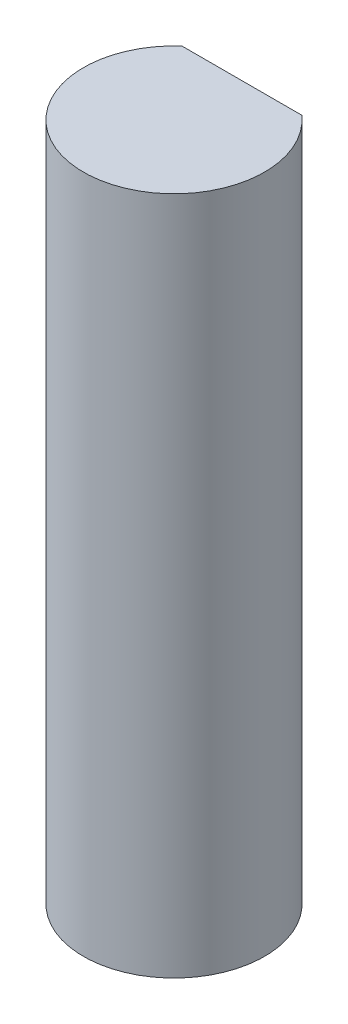
SolidWorks part; units mm, degrees
ref_plane "Front Plane" through (0, 0, 0) normal (0, 0, 1) x (1, 0, 0)
ref_plane "Top Plane" through (0, 0, 0) normal (0, 1, 0) x (1, 0, 0)
ref_plane "Right Plane" through (0, 0, 0) normal (1, 0, 0) x (0, 0, -1)
sketch "Sketch1" plane through (0, 0, 0) normal (0, 1, 0) x (1, 0, 0)
  line L0 (-1.3229, 1.5) -> (1.3229, 1.5)
  line L2 (0, 0) -> (3.486, 0) construction
  arc A0 (-1.3229, 1.5) -> (1.3229, 1.5) centre (0, 0) ccw
  dimension "D1" = 2
  dimension "D2" = 1.5
extrude "Boss-Extrude1" add sketch "Sketch1" along normal blind 15
